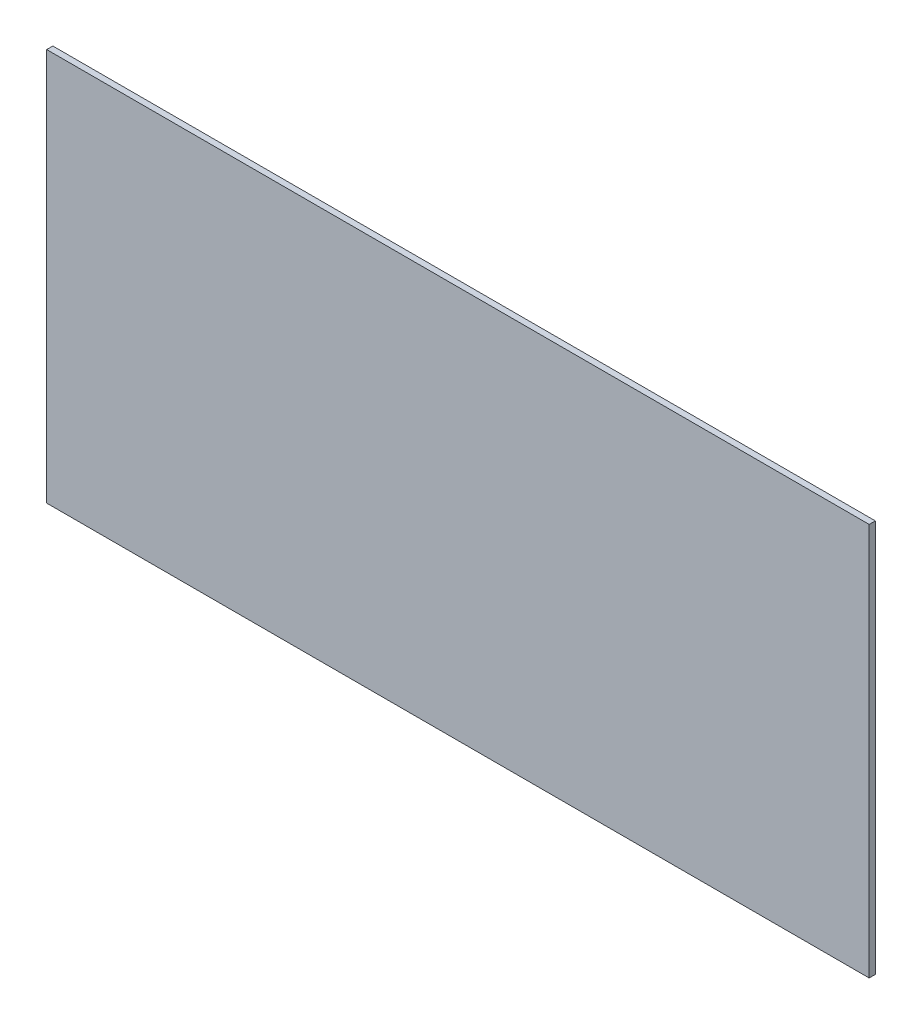
SolidWorks part; units mm, degrees
ref_plane "Płaszczyzna przednia" through (0, 0, 0) normal (0, 0, 1) x (1, 0, 0)
ref_plane "Płaszczyzna górna" through (0, 0, 0) normal (0, 1, 0) x (1, 0, 0)
ref_plane "Płaszczyzna prawa" through (0, 0, 0) normal (1, 0, 0) x (0, 0, -1)
sketch "Szkic1" plane through (0, 0, 0) normal (0, 0, 1) x (1, 0, 0)
  line L1 (-604.3, 321.8429) -> (735.7, 321.8429)
  line L2 (-604.3, 321.8429) -> (-604.3, -318.1571)
  line L3 (-604.3, -318.1571) -> (735.7, -318.1571)
  line L4 (735.7, 321.8429) -> (735.7, -318.1571)
  dimension "D1" = 1340
  dimension "D2" = 640
extrude "Dodanie-wyciągnięcie1" add sketch "Szkic1" along normal blind 10
